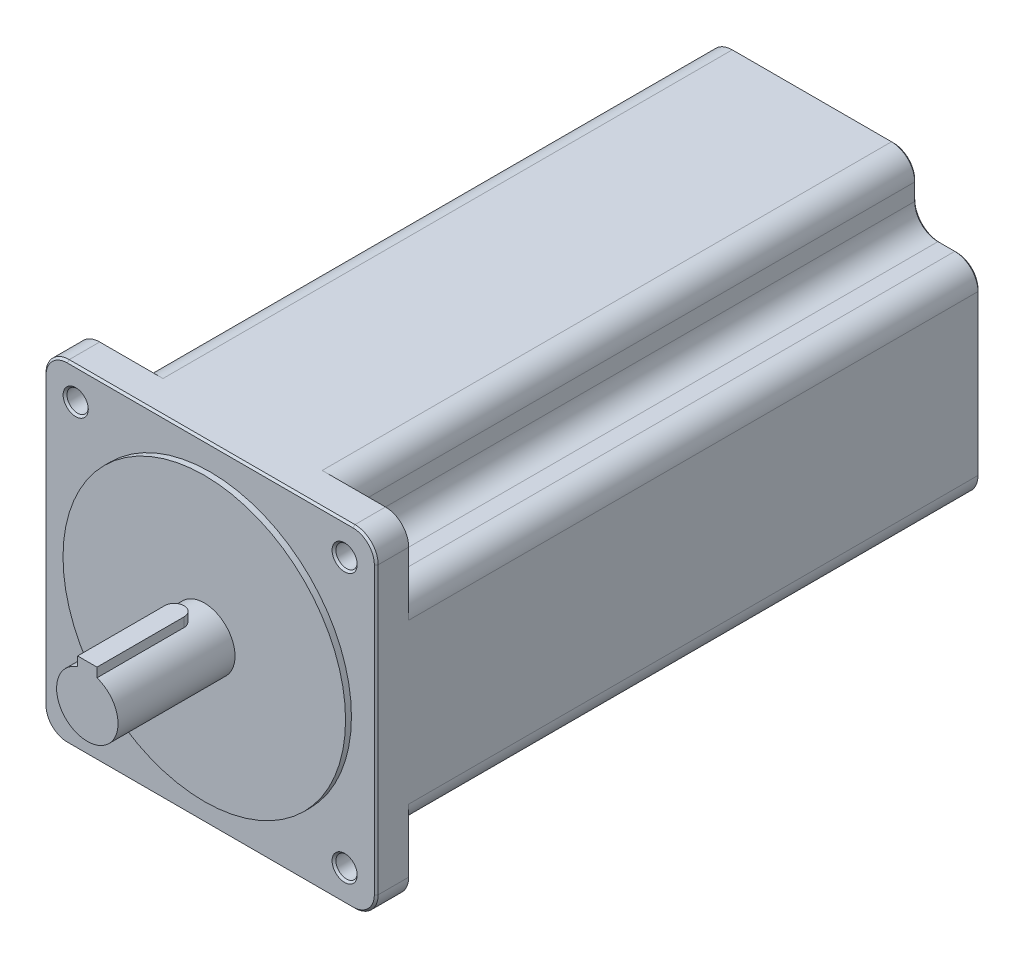
SolidWorks part; units mm, degrees
ref_plane "Front Plane" through (0, 0, 0) normal (0, 0, 1) x (1, 0, 0)
ref_plane "Top Plane" through (0, 0, 0) normal (0, 1, 0) x (1, 0, 0)
ref_plane "Right Plane" through (0, 0, 0) normal (1, 0, 0) x (0, 0, -1)
sketch "Sketch1" plane through (0, 0, 0) normal (0, 0, 1) x (1, 0, 0)
  line L1 (-42.925, -42.925) -> (42.925, -42.925)
  line L2 (-42.925, -42.925) -> (-42.925, 42.925)
  line L3 (-42.925, 42.925) -> (42.925, 42.925)
  line L4 (42.925, -42.925) -> (42.925, 42.925)
  line L5 (-42.925, -42.925) -> (42.925, 42.925) construction
  line L6 (-42.925, 42.925) -> (42.925, -42.925) construction
  line L11 (-34.75, -34.75) -> (34.75, 34.75) construction
  line L12 (-34.75, 34.75) -> (34.75, -34.75) construction
  point P0 (0, 0)
  point P6 (0, 0)
  point P12 (-34.75, 34.75)
  point P13 (34.75, 34.75)
  point P14 (34.75, -34.75)
  point P15 (-34.75, -34.75)
extrude "Boss-Extrude1" add sketch "Sketch1" against normal blind 8.38
sketch "Sketch2" plane through (0, 0, -8.38) normal (0, 0, -1) x (-1, 0, 0)
  line L1 (-26.575, -42.925) -> (26.575, -42.925)
  line L2 (-42.925, -26.575) -> (-42.925, 26.575)
  line L3 (-26.575, 42.925) -> (26.575, 42.925)
  line L4 (42.925, -26.575) -> (42.925, 26.575)
  line L5 (-26.575, -26.575) -> (26.575, 26.575) construction
  line L7 (-26.575, -34.75) -> (26.575, -34.75) construction
  line L8 (-34.75, -26.575) -> (-34.75, 26.575) construction
  line L9 (-26.575, 34.75) -> (26.575, 34.75) construction
  line L10 (34.75, -26.575) -> (34.75, 26.575) construction
  line L11 (-26.575, -26.575) -> (26.575, 26.575) construction
  line L12 (-26.575, 26.575) -> (26.575, -26.575) construction
  line L13 (-26.575, 26.575) -> (-42.925, 26.575)
  line L14 (-26.575, 26.575) -> (-26.575, 42.925)
  line L19 (26.575, 26.575) -> (42.925, 26.575)
  line L20 (26.575, 26.575) -> (26.575, 42.925)
  line L25 (26.575, -26.575) -> (42.925, -26.575)
  line L26 (26.575, -26.575) -> (26.575, -42.925)
  line L31 (-26.575, -26.575) -> (-42.925, -26.575)
  line L32 (-26.575, -26.575) -> (-26.575, -42.925)
  point P0 (0, 0)
  point P3 (0, 0)
  point P7 (0, 0)
extrude "Boss-Extrude3" add sketch "Sketch2" along normal blind 147.62
fillet "Fillet4" radius 6 12 edges at (26.575, -26.575, -82.19) (-26.575, -26.575, -82.19) (-26.575, 26.575, -82.19) (26.575, 26.575, -82.19)
fillet "Fillet5" radius 6 4 edges at (-42.925, -42.925, -4.19) (42.925, -42.925, -4.19) (42.925, 42.925, -4.19) (-42.925, 42.925, -4.19)
sketch "Sketch4" plane through (0, 0, 0) normal (0, 0, 1) x (1, 0, 0)
  circle A0 centre (0, 0) radius 36.51
extrude "Boss-Extrude4" add sketch "Sketch4" along normal blind 1.52
sketch "Sketch5" plane through (0, 0, 1.52) normal (0, 0, 1) x (1, 0, 0)
  circle A0 centre (0, 0) radius 7.9375
extrude "Boss-Extrude5" add sketch "Sketch5" along normal blind 30.23
ref_plane "Plane1" through (0, 9.9375, 0) normal (0, 1, 0) x (1, 0, 0)
sketch "Sketch6" plane through (0, 9.9375, 0) normal (0, 1, 0) x (1, 0, 0)
  line L0 (-7.9375, -31.75) -> (7.9375, -31.75) construction
  line L2 (-2.5, -31.75) -> (2.5, -31.75)
  line L3 (-2.5, -31.75) -> (-2.5, -9.25)
  line L5 (2.5, -31.75) -> (2.5, -9.25)
  arc A0 (2.5, -9.25) -> (-2.5, -9.25) centre (0, -9.25) ccw
  point P0 (0, -31.75)
  point P7 (0, -6.75)
extrude "Boss-Extrude6" add sketch "Sketch6" against normal blind 5
hole_wizard "Ø5.0mm Dowel Hole1" positions "Sketch8" profile "Sketch9" hole size "Ø5.0" standard "ANSI Metric" end condition up to next
sketch "Sketch8" plane through (0, 0, 0) normal (0, 0, 1) x (1, 0, 0)
  point P0 (-34.75, 34.75)
  point P3 (34.75, 34.75)
  point P6 (34.75, -34.75)
  point P9 (-34.75, -34.75)
sketch "Sketch9" plane through (-34.75, 34.75, 0) normal (1, 0, 0) x (0, -1, 0)
  line L0 (0, 0) -> (0, 8.38)
  line L1 (0, 8.38) -> (2.75, 8.38)
  line L2 (2.75, 8.38) -> (2.75, 0)
  line L5 (2.75, 0) -> (0, 0)
  line L11 (0, -6.35) -> (0, 107.95) construction
  dimension "Thru Hole Dia." = 5.5
  dimension "Thru Hole Depth" = 8.38
chamfer "Chamfer1" distance 0.5 angle 45 40 edges at (41.1676, 24.8176, -156) (34.75, 26.575, -156) (28.3324, 28.3324, -156) (26.575, 34.75, -156) (24.8176, 41.1676, -156) (0, 42.925, -156) (-24.8176, 41.1676, -156) (-26.575, 34.75, -156) (-28.3324, 28.3324, -156) (-34.75, 26.575, -156) (-41.1676, 24.8176, -156) (-42.925, 0, -156) (-41.1676, -24.8176, -156) (-34.75, -26.575, -156) (-28.3324, -28.3324, -156) (-26.575, -34.75, -156) (-24.8176, -41.1676, -156) (0, -42.925, -156) (24.8176, -41.1676, -156) (26.575, -34.75, -156) (28.3324, -28.3324, -156) (34.75, -26.575, -156) (41.1676, -24.8176, -156) (42.925, 0, -156) (-37.5, 34.75, -8.38) (-32, 34.75, 0) (32, 34.75, -8.38) (37.5, 34.75, 0) (32, -34.75, -8.38) (37.5, -34.75, 0) (-37.5, -34.75, -8.38) (-32, -34.75, 0) (42.925, 0, 0) (41.1676, 41.1676, 0) (41.1676, -41.1676, 0) (0, 42.925, 0) (0, -42.925, 0) (-41.1676, 41.1676, 0) (-41.1676, -41.1676, 0) (-42.925, 0, 0)
